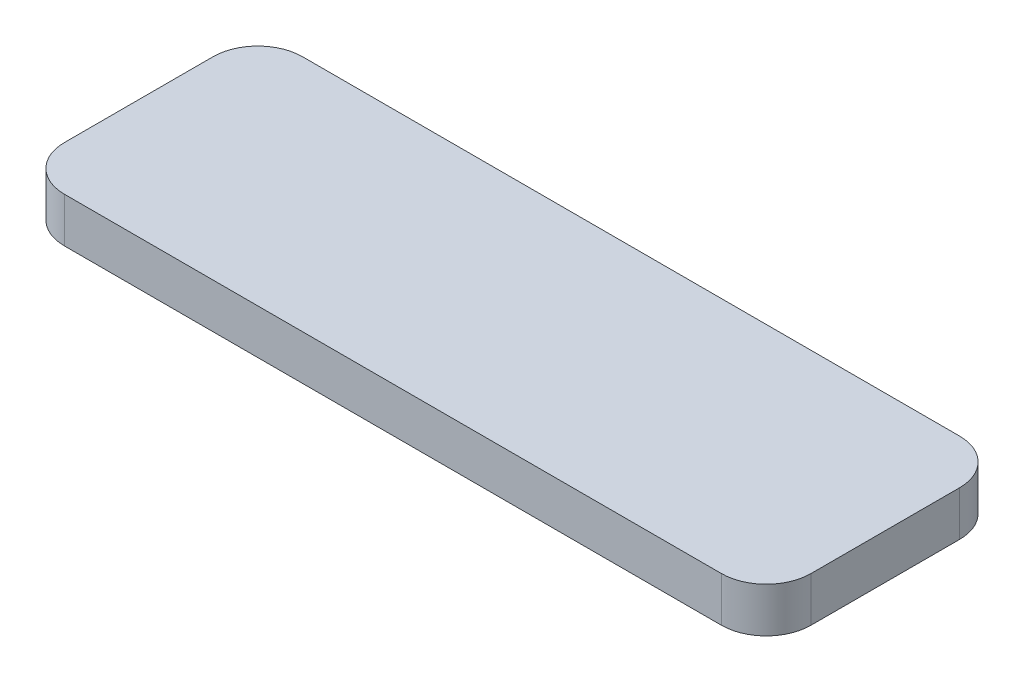
SolidWorks part; units mm, degrees
material "ABS"
ref_plane "Front Plane" through (0, 0, 0) normal (0, 0, 1) x (1, 0, 0)
ref_plane "Top Plane" through (0, 0, 0) normal (0, 1, 0) x (1, 0, 0)
ref_plane "Right Plane" through (0, 0, 0) normal (1, 0, 0) x (0, 0, -1)
sketch "Sketch1" plane through (0, 0, 0) normal (0, 1, 0) x (1, 0, 0)
  line L1 (0, 0) -> (50, 0)
  line L2 (0, 0) -> (0, 15.95)
  line L3 (0, 15.95) -> (50, 15.95)
  line L4 (50, 0) -> (50, 15.95)
  dimension "D1" = 15.95
  dimension "D2" = 50
extrude "Boss-Extrude1" add sketch "Sketch1" along normal blind 3
fillet "Fillet1" radius 3 4 edges at (50, 1.5, 0) (50, 1.5, -15.95) (0, 1.5, 0) (0, 1.5, -15.95)
